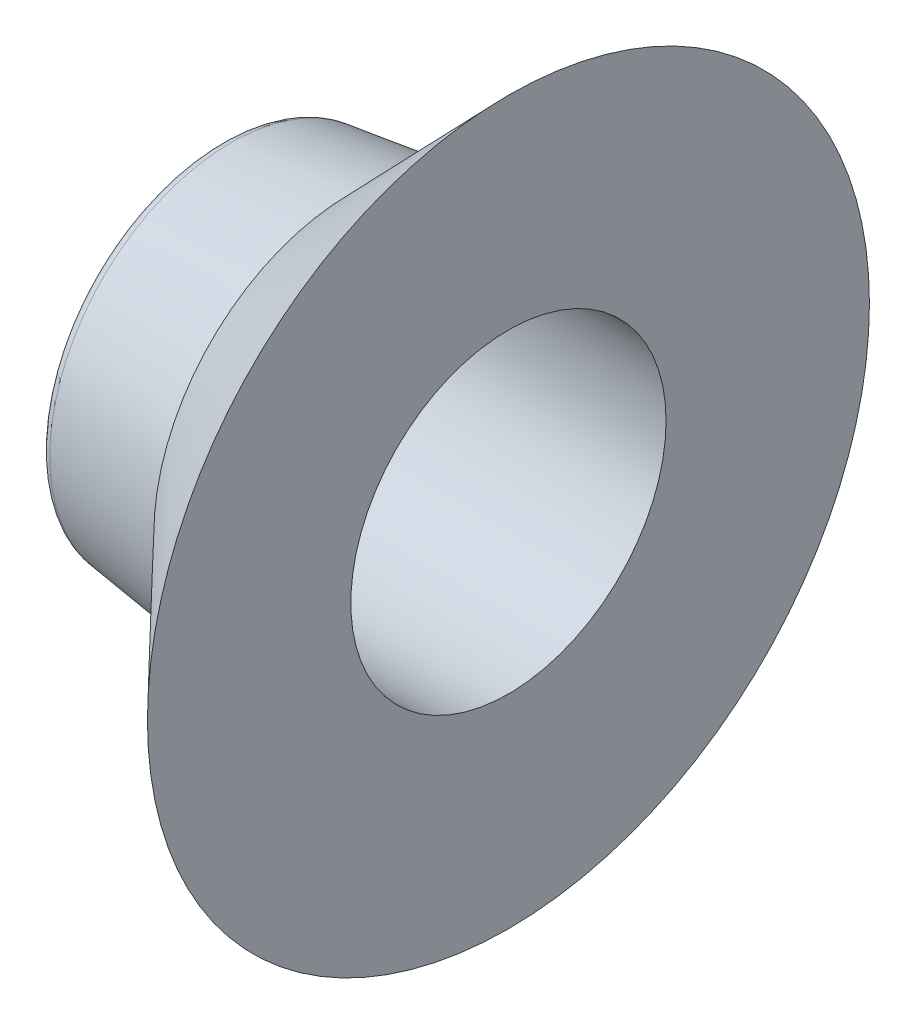
SolidWorks part; units mm, degrees
ref_plane "Front Plane" through (0, 0, 0) normal (0, 0, 1) x (1, 0, 0)
ref_plane "Top Plane" through (0, 0, 0) normal (0, 1, 0) x (1, 0, 0)
ref_plane "Right Plane" through (0, 0, 0) normal (1, 0, 0) x (0, 0, -1)
sketch "Sketch1" plane through (0, 0, 0) normal (0, 0, 1) x (1, 0, 0)
  line L0 (-12.517, -31.877) -> (-17.216, -31.877) construction
  line L1 (-12.517, -31.877) -> (-17.216, -31.877) construction
  line L2 (-17.216, -38.227) -> (-12.517, -38.227) construction
  line L3 (-17.216, -38.227) -> (-12.517, -38.227) construction
  line L4 (-17.216, -31.877) -> (-17.216, -38.227) construction
  line L5 (-12.517, -38.227) -> (-12.517, -31.877) construction
  line L6 (-17.216, -31.877) -> (-17.216, -38.227) construction
  line L7 (-12.517, -38.227) -> (-12.517, -31.877) construction
  line L8 (-14.8665, -31.877) -> (-14.8665, -38.227) construction
  line L9 (-12.517, -35.052) -> (-17.216, -35.052) construction
  line L10 (-9.977, -29.2354) -> (-12.517, -31.877)
  line L13 (-9.977, -32.512) -> (-9.977, -29.2354)
  line L14 (-9.977, -32.512) -> (-14.4224, -32.512)
  line L15 (-14.6125, -32.334) -> (-14.6125, -35.052) construction
  line L16 (-12.517, -31.877) -> (-14.4474, -32.1326)
  arc A0 (-14.4474, -32.1326) -> (-14.4224, -32.512) centre (-14.4224, -32.3215) ccw
  point P11 (7.449, -26.5794)
  point P14 (-14.4349, -32.3215)
  point P19 (0, 0)
  point P20 (0, 0)
  point P21 (-14.5293, -32.4792)
  point P22 (-12.5806, -31.9438)
  dimension "D3" = 0.1905
  dimension "D1" = 11.6332
  dimension "D2" = 5.08
  dimension "D4" = 0.254
  dimension "D5" = 2.54
revolve "Revolve1" add sketch "Sketch1" angle 360 about L9
equation "\"D1@Sketch1\"=.438+.02"
equation "\"D2@Sketch1\"=.19+.01"
